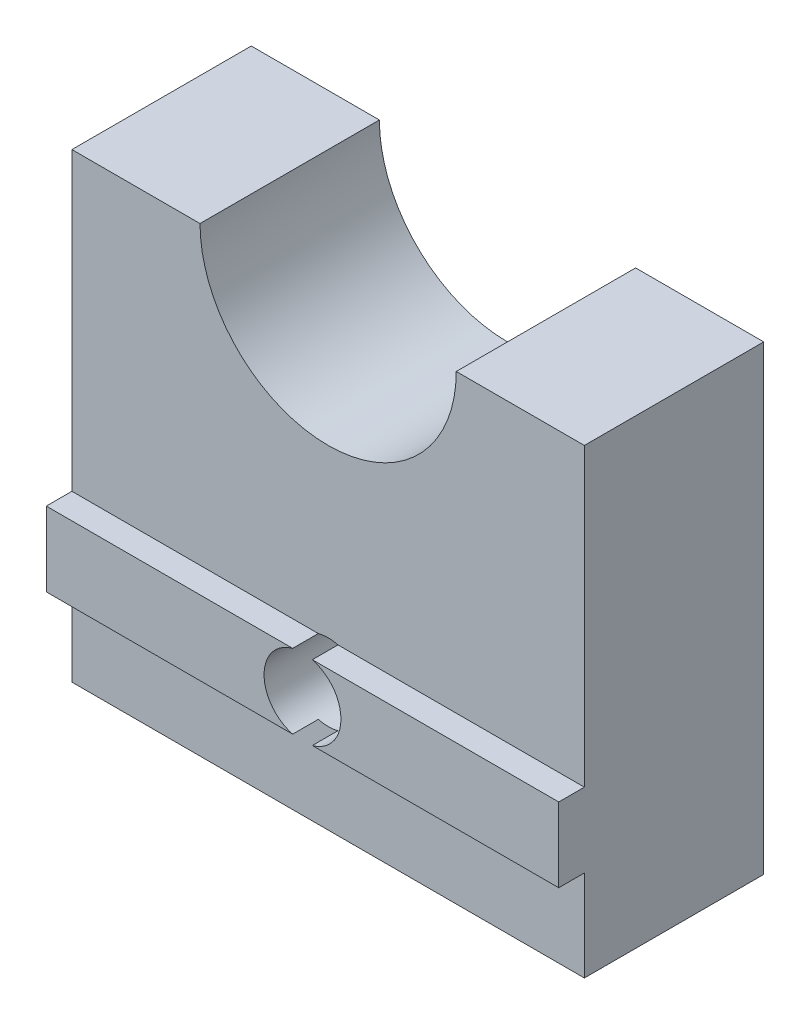
SolidWorks part; units mm, degrees
ref_plane "Front Plane" through (0, 0, 0) normal (0, 0, 1) x (1, 0, 0)
ref_plane "Top Plane" through (0, 0, 0) normal (0, 1, 0) x (1, 0, 0)
ref_plane "Right Plane" through (0, 0, 0) normal (1, 0, 0) x (0, 0, -1)
sketch "Sketch1" plane through (0, 0, 0) normal (0, 0, 1) x (1, 0, 0)
  line L0 (-10, 0) -> (10, 0)
  line L1 (10, 0) -> (10, 18)
  line L2 (10, 18) -> (5, 18)
  line L3 (-5, 18) -> (-10, 18)
  line L4 (-10, 18) -> (-10, 0)
  arc A0 (-5, 18) -> (5, 18) centre (0, 18) ccw
  point P7 (0, 0)
  point P8 (0, 0)
  point P9 (0, 24.9417)
  point P10 (-6.8454, 17.4763)
  dimension "D1" = 20
  dimension "D2" = 18
  dimension "D3" = 5
  dimension "D4" = 18
extrude "Boss-Extrude1" add sketch "Sketch1" along normal blind 7
sketch "Sketch2" plane through (-10, 0, 0) normal (-1, 0, 0) x (0, 0, 1)
  line L0 (7, 18) -> (7, 0) construction
  line L1 (7, 6.45) -> (8, 6.45)
  line L2 (7, 6.45) -> (7, 3.55)
  line L3 (7, 3.55) -> (8, 3.55)
  line L4 (8, 6.45) -> (8, 3.55)
  line L5 (7, 0) -> (0, 0) construction
  dimension "D1" = 1
  dimension "D2" = 2.9
  dimension "D3" = 3.55
extrude "Boss-Extrude2" add sketch "Sketch2" against normal up to surface (20 mm away) up to face at (10, 9, 3.5)
sketch "Sketch3" plane through (0, 0, 8) normal (0, 0, 1) x (1, 0, 0)
  circle A0 centre (0, 5) radius 1.5
  point P2 (0, 0)
  dimension "D1" = 3
  dimension "D2" = 5
extrude "Cut-Extrude1" cut sketch "Sketch3" against normal through all
